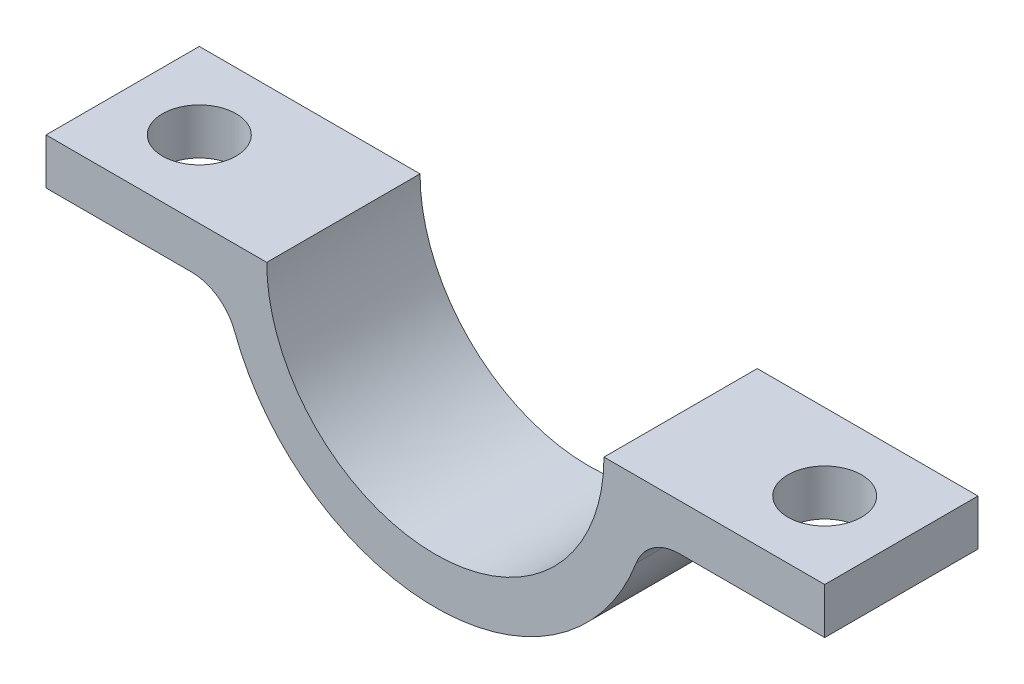
SolidWorks part; units mm, degrees
material "6061-T6 (SS)"
ref_plane "Front Plane" through (0, 0, 0) normal (0, 0, 1) x (1, 0, 0)
ref_plane "Top Plane" through (0, 0, 0) normal (0, 1, 0) x (1, 0, 0)
ref_plane "Right Plane" through (0, 0, 0) normal (1, 0, 0) x (0, 0, -1)
sketch "Sketch1" plane through (0, 0, 0) normal (0, 0, 1) x (1, 0, 0)
  line L0 (0, 0) -> (0, -8.856) construction
  line L1 (5.5, 0) -> (12.7, 0)
  line L2 (12.7, 0) -> (12.7, -1.5)
  line L3 (12.7, -1.5) -> (6.8374, -1.5)
  line L4 (-12.7, -1.5) -> (-6.8374, -1.5)
  line L5 (-12.7, 0) -> (-12.7, -1.5)
  line L6 (-5.5, 0) -> (-12.7, 0)
  arc A0 (-6.8374, -1.5) -> (6.8374, -1.5) centre (0, 0) ccw
  arc A1 (-5.5, 0) -> (5.5, 0) centre (0, 0) ccw
  dimension "D1" = 5.5
  dimension "D2" = 7
  dimension "D3" = 1.5
  dimension "D4" = 12.7
extrude "Boss-Extrude1" add sketch "Sketch1" along normal mid plane 5
sketch "Sketch2" plane through (0, 0, 0) normal (0, 1, 0) x (1, 0, 0)
  line L0 (0, 0) -> (-12.7, 0) construction
  line L1 (-12.7, -2.5) -> (-12.7, 2.5) construction
  line L2 (0, 0) -> (0, 6.0321) construction
  circle A0 centre (-10.2, 0) radius 1.2
  circle A1 centre (10.2, 0) radius 1.2
  dimension "D1" = 2.4
  dimension "D2" = 2.5
extrude "Cut-Extrude1" cut sketch "Sketch2" against normal through all
fillet "Fillet1" radius 1.5 2 edges at (6.8374, -1.5, 0) (-6.8374, -1.5, 0)
